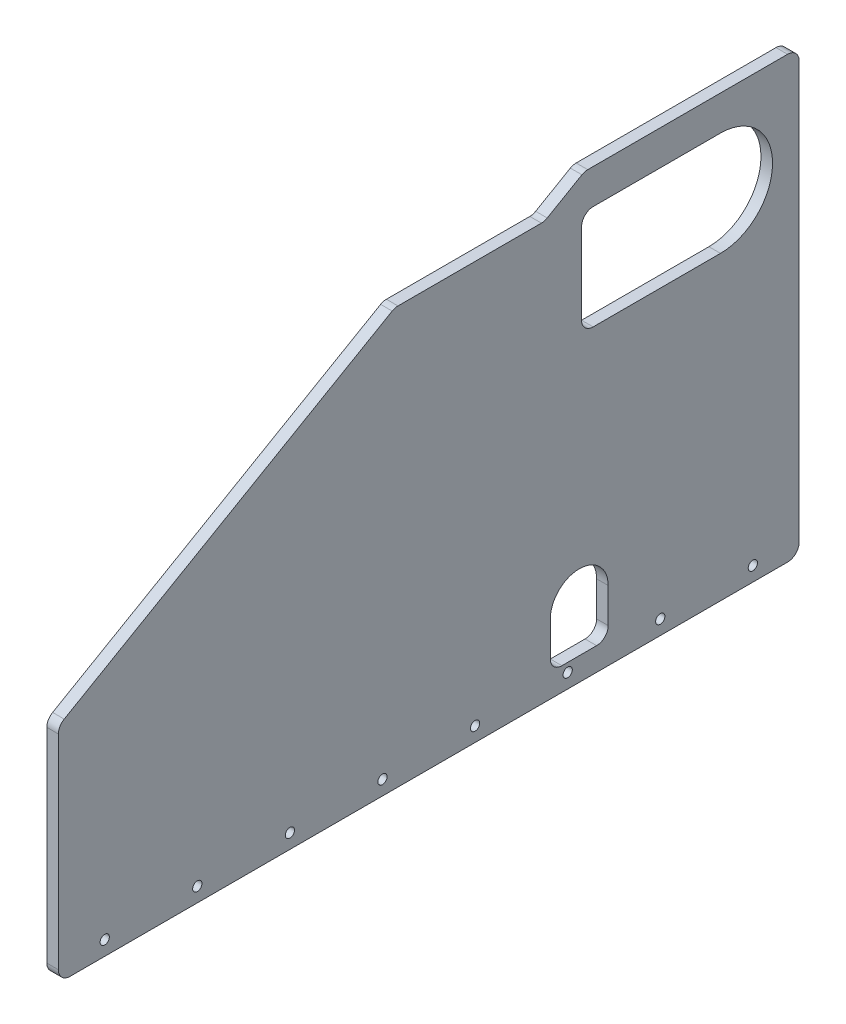
SolidWorks part; units mm, degrees
material "Acrylic (Medium-high impact)"
ref_plane "Front Plane" through (0, 0, 0) normal (0, 0, 1) x (1, 0, 0)
ref_plane "Top Plane" through (0, 0, 0) normal (0, 1, 0) x (1, 0, 0)
ref_plane "Right Plane" through (0, 0, 0) normal (1, 0, 0) x (0, 0, -1)
sketch "Sketch2" plane through (0, 0, 0) normal (1, 0, 0) x (0, 0, -1)
  line L0 (0, 0) -> (0, 294.4501)
  line L1 (0, 294.4501) -> (215.9, 419.1)
  line L2 (215.9, 419.1) -> (431.8, 419.1)
  line L3 (431.8, 419.1) -> (431.8, 0)
  line L4 (431.8, 0) -> (241.3, 0)
  line L5 (241.3, 0) -> (241.3, 38.1)
  line L6 (241.3, 38.1) -> (127, 38.1)
  line L7 (127, 38.1) -> (127, 0)
  line L8 (127, 0) -> (0, 0)
  dimension "D1" = 431.8
  dimension "D2" = 419.1
  dimension "D3" = 127
  dimension "D4" = 114.3
  dimension "D5" = 38.1
  dimension "D6" = 215.9
  dimension "D7" = 150
extrude "Boss-Extrude1" add sketch "Sketch2" along normal blind 6.35 contours L1 L2 L3 L4 L5 L6 L7 L8 L0
sketch "Sketch3" plane through (6.35, 0, 0) normal (1, 0, 0) x (0, 0, -1)
  line L0 (0, 38.1) -> (431.8, 38.1) construction
  line L1 (0, 0) -> (0, 294.4501) construction
  line L2 (431.8, 419.1) -> (431.8, 0) construction
  circle A0 centre (63.5, 38.1) radius 3.9687
  circle A1 centre (368.3, 38.1) radius 3.9688
  dimension "D4" = 7.9375
  dimension "D5" = 7.9375
  dimension "D1" = 38.1
  dimension "D2" = 63.5
  dimension "D3" = 63.5
extrude "Cut-Extrude1" cut sketch "Sketch3" against normal through all
sketch "Sketch4" plane through (6.35, 0, 0) normal (1, 0, 0) x (0, 0, -1)
  line L0 (431.8, 419.1) -> (431.8, 0) construction
  line L1 (215.9, 419.1) -> (431.8, 419.1) construction
  line L2 (393.7, 400.05) -> (393.7, 19.05) construction
  line L4 (393.7, 400.05) -> (330.2, 400.05) construction
  line L5 (330.2, 400.05) -> (330.2, 19.05) construction
  line L6 (330.2, 400.05) -> (330.2, 19.05) construction
  line L7 (330.2, 400.05) -> (323.5506, 19.108) construction
  circle A0 centre (393.7, 400.05) radius 3.175 construction
  circle A1 centre (393.7, 19.05) radius 3.175 construction
  circle A2 centre (323.5506, 19.108) radius 3.175 construction
  circle A3 centre (316.9033, 19.2821) radius 3.175 construction
  circle A4 centre (330.2, 400.05) radius 3.175 construction
  circle A5 centre (330.2, 19.05) radius 3.175 construction
  circle A6 centre (310.26, 19.5721) radius 3.175 construction
  circle A7 centre (303.6228, 19.9781) radius 3.175 construction
  circle A8 centre (296.9937, 20.4998) radius 3.175 construction
  circle A9 centre (290.3747, 21.1372) radius 3.175 construction
  circle A10 centre (283.7678, 21.8899) radius 3.175 construction
  circle A11 centre (277.175, 22.7579) radius 3.175 construction
  circle A12 centre (270.5985, 23.7407) radius 3.175 construction
  dimension "D1" = 6.35
  dimension "D2" = 38.1
  dimension "D3" = 19.05
  dimension "D4" = 381
  dimension "D5" = 10
  dimension "D6" = 1
  dimension "D7" = 101.6
sketch "Sketch5" plane through (6.35, 0, 0) normal (1, 0, 0) x (0, 0, -1)
  line L0 (431.8, 419.1) -> (431.8, 0) construction
  line L1 (431.8, 12.7) -> (425.45, 12.7)
  line L2 (431.8, 12.7) -> (431.8, 25.4)
  line L3 (431.8, 25.4) -> (425.45, 25.4)
  line L4 (425.45, 12.7) -> (425.45, 25.4)
  line L5 (431.8, 0) -> (241.3, 0) construction
  dimension "D1" = 6.35
  dimension "D2" = 12.7
  dimension "D3" = 12.7
extrude "Cut-Extrude3" cut sketch "Sketch5" against normal through all
pattern_linear "LPattern1" count 16 spacing 25.4 along (0, 1, 0) of "Cut-Extrude3"
sketch "Sketch6" plane through (6.35, 0, 0) normal (1, 0, 0) x (0, 0, -1)
  line L0 (0, 0) -> (0, 294.4501) construction
  line L1 (0, 12.7) -> (6.35, 12.7)
  line L2 (0, 12.7) -> (0, 25.4)
  line L3 (0, 25.4) -> (6.35, 25.4)
  line L4 (6.35, 12.7) -> (6.35, 25.4)
  line L5 (425.45, 12.7) -> (431.8, 12.7) construction
  line L6 (425.45, 25.4) -> (425.45, 12.7) construction
  line L7 (127, 0) -> (0, 0) construction
  dimension "D1" = 12.7
extrude "Cut-Extrude4" cut sketch "Sketch6" against normal through all
pattern_linear "LPattern2" count 11 spacing 25.4 along (0, 1, 0) of "Cut-Extrude4"
sketch "Sketch7" plane through (6.35, 0, 0) normal (1, 0, 0) x (0, 0, -1)
  line L0 (127, 38.1) -> (127, 0) construction
  line L1 (127, 12.7) -> (120.65, 12.7)
  line L2 (127, 12.7) -> (127, 25.4)
  line L3 (127, 25.4) -> (120.65, 25.4)
  line L4 (120.65, 12.7) -> (120.65, 25.4)
  line L5 (241.3, 38.1) -> (127, 38.1) construction
  line L6 (127, 38.1) -> (139.7, 38.1)
  line L7 (127, 38.1) -> (127, 44.45)
  line L8 (127, 44.45) -> (139.7, 44.45)
  line L9 (139.7, 38.1) -> (139.7, 44.45)
  line L10 (241.3, 0) -> (241.3, 38.1) construction
  line L11 (152.4, 38.1) -> (165.1, 38.1)
  line L12 (152.4, 38.1) -> (152.4, 44.45)
  line L13 (152.4, 44.45) -> (165.1, 44.45)
  line L14 (165.1, 38.1) -> (165.1, 44.45)
  line L15 (177.8, 38.1) -> (190.5, 38.1)
  line L16 (177.8, 38.1) -> (177.8, 44.45)
  line L17 (177.8, 44.45) -> (190.5, 44.45)
  line L18 (190.5, 38.1) -> (190.5, 44.45)
  line L19 (241.3, 25.4) -> (247.65, 25.4)
  line L20 (241.3, 25.4) -> (241.3, 12.7)
  line L21 (241.3, 12.7) -> (247.65, 12.7)
  line L22 (247.65, 25.4) -> (247.65, 12.7)
  line L23 (0, 12.7) -> (6.35, 12.7) construction
  line L24 (6.35, 12.7) -> (6.35, 25.4) construction
  line L25 (127, 0) -> (0, 0) construction
  line L26 (431.8, 0) -> (241.3, 0) construction
  line L27 (203.2, 44.45) -> (215.9, 44.45)
  line L28 (203.2, 44.45) -> (203.2, 38.1)
  line L29 (203.2, 38.1) -> (215.9, 38.1)
  line L30 (215.9, 44.45) -> (215.9, 38.1)
  line L32 (241.3, 38.1) -> (228.6, 38.1)
  line L33 (241.3, 38.1) -> (241.3, 44.45)
  line L34 (241.3, 44.45) -> (228.6, 44.45)
  line L35 (228.6, 38.1) -> (228.6, 44.45)
  dimension "D1" = 12.7
  dimension "D2" = 12.7
  dimension "D4" = 12.7
  dimension "D5" = 12.7
  dimension "D6" = 12.7
extrude "Cut-Extrude5" cut sketch "Sketch7" against normal through all
sketch "Sketch8" plane through (6.35, 0, 0) normal (1, 0, 0) x (0, 0, -1)
  line L0 (201.9351, 411.0373) -> (212.9336, 417.3873)
  line L1 (201.9351, 411.0373) -> (205.1101, 405.5381)
  line L2 (212.9336, 417.3873) -> (216.1086, 411.8881)
  line L3 (205.1101, 405.5381) -> (216.1086, 411.8881)
  line L4 (0, 294.4501) -> (215.9, 419.1) construction
  line L5 (6.35, 279.4) -> (0, 279.4) construction
  line L6 (6.35, 266.7) -> (6.35, 279.4) construction
  line L7 (216.1086, 411.8881) -> (7.1367, 291.2381) construction
  line L8 (6.35, 279.4) -> (6.35, 292.1) construction
  line L9 (215.9, 412.75) -> (215.6832, 412.6248) construction
  line L10 (7.1367, 291.2381) -> (3.9617, 296.7373) construction
  line L11 (6.35, 292.1) -> (6.5668, 292.2252) construction
  line L12 (215.9, 419.1) -> (215.9, 412.75) construction
  line L13 (215.9, 419.1) -> (431.8, 419.1) construction
  dimension "D1" = 215.9
  dimension "D2" = 241.3
  dimension "D3" = 6.35
extrude "Cut-Extrude6" cut sketch "Sketch8" against normal through all
pattern_linear "LPattern3" count 10 spacing 25.4 along (0, -0.5, 0.866) of "Cut-Extrude6"
sketch "Sketch9" plane through (6.35, 0, 0) normal (1, 0, 0) x (0, 0, -1)
  line L0 (215.9, 419.1) -> (431.8, 419.1) construction
  line L1 (419.1, 419.1) -> (406.4, 419.1)
  line L2 (419.1, 419.1) -> (419.1, 412.75)
  line L3 (419.1, 412.75) -> (406.4, 412.75)
  line L4 (406.4, 419.1) -> (406.4, 412.75)
  line L5 (431.8, 406.4) -> (425.45, 406.4) construction
  line L6 (425.45, 406.4) -> (425.45, 393.7) construction
  line L7 (431.8, 419.1) -> (431.8, 406.4) construction
  dimension "D1" = 12.7
extrude "Cut-Extrude7" cut sketch "Sketch9" against normal through all
pattern_linear "LPattern4" count 8 spacing 25.4 along (0, 0, 1) of "Cut-Extrude7"
sketch "Sketch10" plane through (6.35, 0, 0) normal (1, 0, 0) x (0, 0, -1)
  line L0 (127, 0) -> (0, 0) construction
  line L1 (146.05, 273.05) -> (222.25, 273.05) construction
  line L2 (146.05, 273.05) -> (146.05, 57.15) construction
  line L3 (146.05, 57.15) -> (222.25, 57.15) construction
  line L4 (222.25, 273.05) -> (222.25, 57.15) construction
  line L5 (146.05, 273.05) -> (19.05, 273.05) construction
  line L6 (146.05, 273.05) -> (146.05, 247.65) construction
  line L7 (146.05, 247.65) -> (19.05, 247.65) construction
  line L8 (19.05, 273.05) -> (19.05, 247.65) construction
  line L9 (0, 254) -> (0, 266.7) construction
  line L10 (127, 44.45) -> (127, 25.4) construction
  line L11 (241.3, 25.4) -> (241.3, 44.45) construction
  line L12 (152.4, 38.1) -> (139.7, 38.1) construction
  circle A0 centre (222.25, 273.05) radius 3.175
  circle A1 centre (222.25, 57.15) radius 3.175
  circle A2 centre (146.05, 57.15) radius 3.175
  circle A3 centre (146.05, 273.05) radius 3.175
  circle A4 centre (19.05, 273.05) radius 3.175 construction
  circle A5 centre (19.05, 247.65) radius 3.175 construction
  circle A6 centre (146.05, 247.65) radius 3.175 construction
  dimension "D4" = 6.35
  dimension "D1" = 273.05
  dimension "D2" = 19.05
  dimension "D3" = 247.65
  dimension "D5" = 19.05
  dimension "D6" = 19.05
  dimension "D7" = 19.05
extrude "Cut-Extrude8" cut sketch "Sketch10" against normal through all
sketch "Sketch11" plane through (6.35, 0, 0) normal (1, 0, 0) x (0, 0, -1)
  line L0 (127, 0) -> (0, 0) construction
  line L1 (0, 254) -> (0, 266.7) construction
  line L5 (241.3, 0) -> (241.3, 12.7) construction
  line L6 (177.8, 38.1) -> (165.1, 38.1) construction
  line L7 (38.1, 260.35) -> (266.7, 260.35) construction
  line L8 (266.7, 260.35) -> (266.7, 63.5) construction
  circle A0 centre (38.1, 260.35) radius 3.9688
  circle A1 centre (266.7, 63.5) radius 3.9688 construction
  circle A2 centre (266.7, 260.35) radius 3.9688
  dimension "D3" = 7.9375
  dimension "D1" = 260.35
  dimension "D2" = 38.1
  dimension "D4" = 25.4
  dimension "D5" = 25.4
extrude "Cut-Extrude9" cut sketch "Sketch11" against normal through all
sketch "Sketch12" plane through (6.35, 0, 0) normal (1, 0, 0) x (0, 0, -1)
  line L0 (127, 50.8) -> (127, 38.1)
  line L1 (120.65, 25.4) -> (127, 25.4)
  line L2 (120.65, 25.4) -> (120.65, 12.7)
  line L3 (120.65, 12.7) -> (127, 12.7)
  line L4 (127, 25.4) -> (127, 12.7)
  line L5 (120.65, 50.8) -> (127, 50.8)
  line L6 (120.65, 50.8) -> (120.65, 38.1)
  line L7 (120.65, 38.1) -> (127, 38.1)
  line L8 (127, 76.2) -> (127, 63.5)
  line L9 (120.65, 76.2) -> (127, 76.2)
  line L10 (120.65, 76.2) -> (120.65, 63.5)
  line L11 (120.65, 63.5) -> (127, 63.5)
  line L12 (127, 101.6) -> (127, 88.9)
  line L13 (120.65, 101.6) -> (127, 101.6)
  line L14 (120.65, 101.6) -> (120.65, 88.9)
  line L15 (120.65, 88.9) -> (127, 88.9)
  line L16 (127, 127) -> (127, 114.3)
  line L17 (120.65, 127) -> (127, 127)
  line L18 (120.65, 127) -> (120.65, 114.3)
  line L19 (120.65, 114.3) -> (127, 114.3)
  line L20 (127, 152.4) -> (127, 139.7) construction
  line L21 (120.65, 152.4) -> (127, 152.4) construction
  line L22 (120.65, 152.4) -> (120.65, 139.7) construction
  line L23 (120.65, 139.7) -> (127, 139.7) construction
  line L24 (127, 177.8) -> (127, 165.1) construction
  line L25 (120.65, 177.8) -> (127, 177.8) construction
  line L26 (120.65, 177.8) -> (120.65, 165.1) construction
  line L27 (120.65, 165.1) -> (127, 165.1) construction
  dimension "D1" = 7
extrude "Cut-Extrude13" cut sketch "Sketch12" against normal through all
sketch "Sketch13" plane through (6.35, 0, 0) normal (1, 0, 0) x (0, 0, -1)
  line L1 (120.65, 25.4) -> (120.65, 12.7) construction
  line L2 (84.65, 117.2) -> (347.15, 117.2) construction
  line L3 (84.65, 117.2) -> (6.35, 117.2) construction
  line L4 (6.35, 114.3) -> (6.35, 127) construction
  line L5 (347.15, 117.2) -> (425.45, 117.2) construction
  line L6 (425.45, 127) -> (425.45, 114.3) construction
  circle A0 centre (84.65, 117.2) radius 20
  circle A1 centre (347.15, 117.2) radius 20
  dimension "D2" = 40
  dimension "D1" = 9.8
  dimension "D3" = 36
sketch "Sketch14" plane through (6.35, 0, 0) normal (1, 0, 0) x (0, 0, -1)
  line L0 (36.9572, 315.7873) -> (47.9558, 322.1373)
  line L1 (36.9572, 315.7873) -> (40.1322, 310.2881)
  line L2 (47.9558, 322.1373) -> (51.1308, 316.6381)
  line L3 (40.1322, 310.2881) -> (51.1308, 316.6381)
  line L4 (80.9513, 341.1873) -> (91.9498, 347.5373)
  line L5 (80.9513, 341.1873) -> (84.1263, 335.6881)
  line L6 (91.9498, 347.5373) -> (95.1248, 342.0381)
  line L7 (84.1263, 335.6881) -> (95.1248, 342.0381)
  line L8 (91.9498, 347.5373) -> (95.1248, 342.0381) construction
extrude "Cut-Extrude15" cut sketch "Sketch14" against normal through all
sketch "Sketch15" plane through (6.35, 0, 0) normal (1, 0, 0) x (0, 0, -1)
  line L0 (43.8866, 319.2853) -> (85.4558, 343.2853) construction
  line L1 (46.8439, 314.1631) -> (53.1939, 303.1646) construction
  line L3 (64.6712, 331.2853) -> (64.4535, 331.6623) construction
  line L4 (58.9543, 328.4873) -> (69.9528, 334.8373) construction
  line L5 (29.1337, 303.9381) -> (62.1293, 322.9881) construction
  line L6 (31.5586, 305.3381) -> (62.1293, 322.9881)
  line L7 (73.1278, 329.3381) -> (103.6985, 346.9881)
  line L8 (73.1278, 329.3381) -> (106.1234, 348.3881) construction
  circle A0 centre (43.8866, 319.2853) radius 18.6147
  circle A1 centre (85.4558, 343.2853) radius 18.6147
  dimension "D2" = 12.7
  dimension "D1" = 48
extrude "Cut-Extrude16" cut sketch "Sketch15" against normal through all contours L6 A0 | L7 A1
sketch "Sketch17" plane through (6.35, 0, 0) normal (1, 0, 0) x (0, 0, -1)
  line L0 (0, 139.7) -> (6.35, 139.7) construction
  line L1 (19.05, 146.05) -> (31.75, 146.05)
  line L2 (19.05, 146.05) -> (19.05, 139.7)
  line L3 (19.05, 139.7) -> (31.75, 139.7)
  line L4 (31.75, 146.05) -> (31.75, 139.7)
  line L5 (6.35, 139.7) -> (6.35, 152.4) construction
  dimension "D1" = 12.7
  dimension "D2" = 6.35
  dimension "D3" = 12.7
extrude "Cut-Extrude17" cut sketch "Sketch17" against normal through all
pattern_linear "LPattern5" count 17 spacing 25.4 along (0, 0, -1) of "Cut-Extrude17"
pattern_linear "LPattern6" count 2 spacing 120.65 along (0, 0, -1) of "Cut-Extrude13"
sketch "Sketch18" plane through (6.35, 0, 0) normal (1, 0, 0) x (0, 0, -1)
  line L1 (127, 120.65) -> (139.7, 120.65)
  line L2 (127, 120.65) -> (127, 114.3)
  line L3 (127, 114.3) -> (139.7, 114.3)
  line L4 (139.7, 120.65) -> (139.7, 114.3)
  dimension "D1" = 12.7
  dimension "D2" = 6.35
extrude "Cut-Extrude18" cut sketch "Sketch18" against normal through all
pattern_linear "LPattern7" count 5 spacing 25.4 along (0, 0, -1) of "Cut-Extrude18"
sketch "Sketch19" plane through (6.35, 0, 0) normal (1, 0, 0) x (0, 0, -1)
  line L0 (25.4, 279.7854) -> (222.7059, 393.7)
  line L1 (222.7059, 393.7) -> (406.4, 393.7)
  line L2 (406.4, 393.7) -> (406.4, 165.1)
  line L3 (406.4, 165.1) -> (25.4, 165.1)
  line L4 (25.4, 165.1) -> (25.4, 279.7854)
  line L5 (0, 228.6) -> (0, 241.3) construction
  line L6 (431.8, 292.1) -> (431.8, 279.4) construction
  line L7 (368.3, 419.1) -> (381, 419.1) construction
  line L9 (146.9425, 379.2873) -> (157.941, 385.6373) construction
  line L10 (124.9454, 366.5873) -> (135.9439, 372.9373) construction
  line L11 (222.25, 139.7) -> (234.95, 139.7) construction
  point P16 (130.4447, 369.7623)
  dimension "D1" = 25.4
  dimension "D2" = 25.4
  dimension "D3" = 25.4
  dimension "D4" = 25.4
  dimension "D5" = 25.4
extrude "Cut-Extrude19" cut sketch "Sketch19" against normal through all
sketch "Sketch20" plane through (6.35, 0, 0) normal (1, 0, 0) x (0, 0, -1)
  line L0 (165.1, 120.65) -> (152.4, 120.65) construction
  line L1 (133.35, 107.95) -> (234.95, 107.95)
  line L2 (133.35, 107.95) -> (133.35, 50.8)
  line L3 (133.35, 50.8) -> (234.95, 50.8)
  line L4 (234.95, 107.95) -> (234.95, 50.8)
  line L5 (120.65, 101.6) -> (120.65, 88.9) construction
  line L6 (177.8, 38.1) -> (165.1, 38.1) construction
  line L7 (247.65, 101.6) -> (247.65, 88.9) construction
  dimension "D1" = 12.7
  dimension "D2" = 12.7
  dimension "D3" = 12.7
  dimension "D4" = 12.7
extrude "Cut-Extrude20" cut sketch "Sketch20" against normal through all
sketch "Sketch21" plane through (6.35, 0, 0) normal (1, 0, 0) x (0, 0, -1)
  line L0 (266.7, 25.4) -> (308.203, 25.4)
  line L1 (25.4, 133.35) -> (25.4, 82.0941)
  line L2 (308.203, 25.4) -> (406.4, 82.0941)
  line L3 (25.4, 82.0941) -> (101.6, 38.1)
  line L4 (406.4, 82.0941) -> (406.4, 133.35)
  line L5 (406.4, 133.35) -> (266.7, 133.35)
  line L6 (266.7, 133.35) -> (266.7, 25.4)
  line L7 (406.4, 165.1) -> (406.4, 393.7) construction
  line L8 (431.8, 0) -> (241.3, 0) construction
  line L9 (241.3, 25.4) -> (241.3, 38.1) construction
  line L10 (387.35, 146.05) -> (374.65, 146.05) construction
  line L11 (101.6, 38.1) -> (101.6, 133.35)
  line L12 (101.6, 133.35) -> (25.4, 133.35)
  line L13 (0, 101.6) -> (0, 114.3) construction
  line L14 (127, 101.6) -> (127, 88.9) construction
  line L20 (25.4, 38.1) -> (25.4, 25.4)
  line L21 (25.4, 25.4) -> (47.397, 25.4)
  line L22 (47.397, 25.4) -> (25.4, 38.1)
  circle A0 centre (63.5, 38.1) radius 3.9687 construction
  circle A1 centre (368.3, 38.1) radius 3.9688 construction
  dimension "D4" = 150
  dimension "D5" = 19.05
  dimension "D9" = 19.05
  dimension "D1" = 25.4
  dimension "D2" = 25.4
  dimension "D3" = 12.7
  dimension "D6" = 25.4
  dimension "D7" = 25.4
  dimension "D8" = 120
  dimension "D12" = 19.05
extrude "Cut-Extrude21" cut sketch "Sketch21" against normal through all
sketch "Sketch22" plane through (6.35, 0, 0) normal (1, 0, 0) x (0, 0, -1)
  line L0 (384.403, 25.4) -> (406.4, 38.1)
  line L1 (406.4, 38.1) -> (406.4, 25.4)
  line L2 (406.4, 25.4) -> (384.403, 25.4)
  line L3 (406.4, 82.0941) -> (406.4, 133.35) construction
  line L4 (266.7, 25.4) -> (308.203, 25.4) construction
  line L5 (358.775, 54.5978) -> (377.825, 21.6022) construction
  line L6 (308.203, 25.4) -> (406.4, 82.0941) construction
  point P11 (368.3, 38.1)
extrude "Cut-Extrude22" cut sketch "Sketch22" against normal through all
sketch "Sketch26" plane through (6.35, 0, 0) normal (1, 0, 0) x (0, 0, -1)
  line L0 (278.9441, 133.35) -> (234.95, 107.95) construction
  line L1 (278.9441, 133.35) -> (275.7691, 138.8493) construction
  line L2 (234.95, 107.95) -> (231.775, 113.4493) construction
  line L3 (275.7691, 138.8493) -> (231.775, 113.4493) construction
  line L4 (406.4, 133.35) -> (266.7, 133.35) construction
  line L5 (228.6, 120.65) -> (228.6, 114.3) construction
  line L6 (308.203, 25.4) -> (406.4, 82.0941) construction
  line L7 (266.7, 133.35) -> (266.7, 126.2809)
  line L8 (266.7, 133.35) -> (266.7, 25.4) construction
  line L9 (266.7, 126.2809) -> (278.9441, 133.35)
  line L10 (278.9441, 133.35) -> (266.7, 133.35)
  line L11 (89.3559, 133.35) -> (101.6, 126.2809)
  line L12 (101.6, 133.35) -> (25.4, 133.35) construction
  line L13 (101.6, 38.1) -> (101.6, 133.35) construction
  line L14 (101.6, 126.2809) -> (101.6, 133.35)
  line L15 (101.6, 133.35) -> (89.3559, 133.35)
  line L16 (25.4, 82.0941) -> (101.6, 38.1) construction
  line L17 (266.7, 32.4691) -> (278.9441, 25.4)
  line L18 (266.7, 133.35) -> (266.7, 25.4) construction
  line L19 (266.7, 25.4) -> (308.203, 25.4) construction
  line L20 (278.9441, 25.4) -> (266.7, 25.4)
  line L21 (266.7, 25.4) -> (266.7, 32.4691)
  line L22 (133.35, 107.95) -> (133.35, 100.8809)
  line L23 (133.35, 107.95) -> (133.35, 50.8) construction
  line L24 (133.35, 100.8809) -> (145.5941, 107.95)
  line L25 (234.95, 107.95) -> (133.35, 107.95) construction
  line L26 (145.5941, 107.95) -> (133.35, 107.95)
  line L27 (234.95, 107.95) -> (222.7059, 107.95)
  line L28 (222.7059, 107.95) -> (234.95, 100.8809)
  line L29 (234.95, 50.8) -> (234.95, 107.95) construction
  line L30 (234.95, 100.8809) -> (234.95, 107.95)
  line L31 (133.35, 50.8) -> (145.5941, 50.8)
  line L32 (133.35, 50.8) -> (234.95, 50.8) construction
  line L33 (145.5941, 50.8) -> (133.35, 57.8691)
  line L34 (133.35, 57.8691) -> (133.35, 50.8)
  line L35 (234.95, 50.8) -> (222.7059, 50.8)
  line L36 (222.7059, 50.8) -> (234.95, 57.8691)
  line L37 (234.95, 57.8691) -> (234.95, 50.8)
extrude "Boss-Extrude4" add sketch "Sketch26" against normal through all
sketch "Sketch27" plane through (6.35, 0, 0) normal (1, 0, 0) x (0, 0, -1)
  line L0 (12.7, 165.1) -> (12.7, 287.1177)
  line L1 (12.7, 287.1177) -> (219.303, 406.4)
  line L2 (219.303, 406.4) -> (419.1, 406.4)
  line L3 (419.1, 406.4) -> (419.1, 165.1)
  line L4 (222.7059, 393.7) -> (25.4, 279.7854) construction
  line L5 (0, 228.6) -> (0, 241.3) construction
  line L6 (14.9602, 303.0873) -> (25.9587, 309.4373) construction
  line L7 (419.1, 165.1) -> (12.7, 165.1)
  line L15 (31.75, 146.05) -> (19.05, 146.05) construction
  line L16 (241.3, 419.1) -> (254, 419.1) construction
  line L17 (431.8, 393.7) -> (431.8, 381) construction
  dimension "D1" = 12.7
  dimension "D2" = 12.7
  dimension "D3" = 12.7
  dimension "D4" = 12.7
  dimension "D8" = 19.05
extrude "Boss-Extrude5" add sketch "Sketch27" against normal blind 6.35 separate body
sketch "Sketch28" plane through (6.35, 0, 0) normal (1, 0, 0) x (0, 0, -1)
  line L0 (251.053, 406.4) -> (273.05, 393.7)
  line L1 (419.1, 406.4) -> (219.303, 406.4) construction
  line L2 (273.05, 393.7) -> (279.4, 393.7)
  line L3 (279.4, 393.7) -> (301.397, 406.4)
  line L4 (301.397, 406.4) -> (251.053, 406.4)
  line L5 (317.5, 419.1) -> (330.2, 419.1) construction
  line L6 (431.8, 393.7) -> (431.8, 381) construction
  dimension "D1" = 30
  dimension "D2" = 30
  dimension "D3" = 25.4
  dimension "D4" = 152.4
  dimension "D5" = 158.75
extrude "Cut-Extrude23" cut sketch "Sketch28" against normal through all
sketch "Sketch29" plane through (6.35, 0, 0) normal (1, 0, 0) x (0, 0, -1)
  line L0 (282.575, 203.2) -> (282.575, 177.8)
  line L1 (282.575, 177.8) -> (314.325, 177.8)
  line L2 (314.325, 177.8) -> (314.325, 203.2)
  line L3 (25.4, 165.1) -> (406.4, 165.1) construction
  line L4 (431.8, 190.5) -> (431.8, 177.8) construction
  arc A0 (282.575, 203.2) -> (314.325, 203.2) centre (298.45, 203.2) cw
  dimension "D2" = 31.75
  dimension "D4" = 25.4
  dimension "D1" = 12.7
  dimension "D3" = 133.35
extrude "Cut-Extrude24" cut sketch "Sketch29" against normal through all
delete or keep bodies "Body-Delete1" type delete bodies bodies 130
fillet "Fillet1" radius 6.35 11 edges at (3.175, 165.1, -12.7) (3.175, 287.1177, -12.7) (3.175, 393.7, -279.4) (3.175, 406.4, -219.303) (3.175, 393.7, -273.05) (3.175, 406.4, -251.053) (3.175, 406.4, -301.397) (3.175, 406.4, -419.1) (3.175, 165.1, -419.1) (3.175, 177.8, -314.325) (3.175, 177.8, -282.575)
sketch "Sketch30" plane through (6.35, 0, 0) normal (1, 0, 0) x (0, 0, -1)
  line L0 (12.7, 173.0375) -> (419.1, 173.0375) construction
  line L1 (12.7, 283.4516) -> (12.7, 171.45) construction
  line L2 (419.1, 171.45) -> (419.1, 400.05) construction
  line L3 (19.05, 165.1) -> (412.75, 165.1) construction
  circle A0 centre (38.1, 173.0375) radius 2.54
  circle A1 centre (88.9, 173.0375) radius 2.54
  circle A2 centre (139.7, 173.0375) radius 2.54
  circle A3 centre (190.5, 173.0375) radius 2.54
  circle A4 centre (241.3, 173.0375) radius 2.54
  circle A5 centre (292.1, 173.0375) radius 2.54
  circle A6 centre (342.9, 173.0375) radius 2.54
  circle A7 centre (393.7, 173.0375) radius 2.54
  dimension "D2" = 25.4
  dimension "D3" = 5.08
  dimension "D1" = 7.9375
  dimension "D4" = 8
extrude "Cut-Extrude25" cut sketch "Sketch30" against normal through all
sketch "Sketch31" plane through (6.35, 0, 0) normal (1, 0, 0) x (0, 0, -1)
  line L0 (412.75, 406.4) -> (303.0985, 406.4) construction
  line L1 (299.725, 330.2) -> (375.925, 330.2)
  line L2 (299.725, 330.2) -> (299.725, 387.35)
  line L3 (299.725, 387.35) -> (375.925, 387.35)
  line L4 (375.925, 330.2) -> (375.925, 387.35)
  line L5 (419.1, 171.45) -> (419.1, 400.05) construction
  dimension "D1" = 19.05
  dimension "D2" = 57.15
  dimension "D3" = 43.175
  dimension "D4" = 76.2
extrude "Cut-Extrude26" cut sketch "Sketch31" against normal through all
sketch "Sketch32" plane through (6.35, 0, 0) normal (1, 0, 0) x (0, 0, -1)
  line L0 (375.925, 330.2) -> (375.925, 387.35) construction
  line L1 (375.925, 387.35) -> (375.925, 330.2)
  arc A0 (375.925, 387.35) -> (375.925, 330.2) centre (375.925, 358.775) cw
extrude "Cut-Extrude27" cut sketch "Sketch32" against normal through all
sketch "Sketch33" plane through (6.35, 0, 0) normal (1, 0, 0) x (0, 0, -1)
  line L1 (274.7515, 393.7) -> (164.3989, 393.7)
  line L2 (274.7515, 393.7) -> (274.7515, 435.8148)
  line L3 (274.7515, 435.8148) -> (164.3989, 435.8148)
  line L4 (164.3989, 393.7) -> (164.3989, 435.8148)
extrude "Cut-Extrude28" cut sketch "Sketch33" against normal through all
fillet "Fillet2" radius 6.35 3 edges at (3.175, 393.7, -197.3059) (3.175, 330.2, -299.725) (3.175, 387.35, -299.725)
